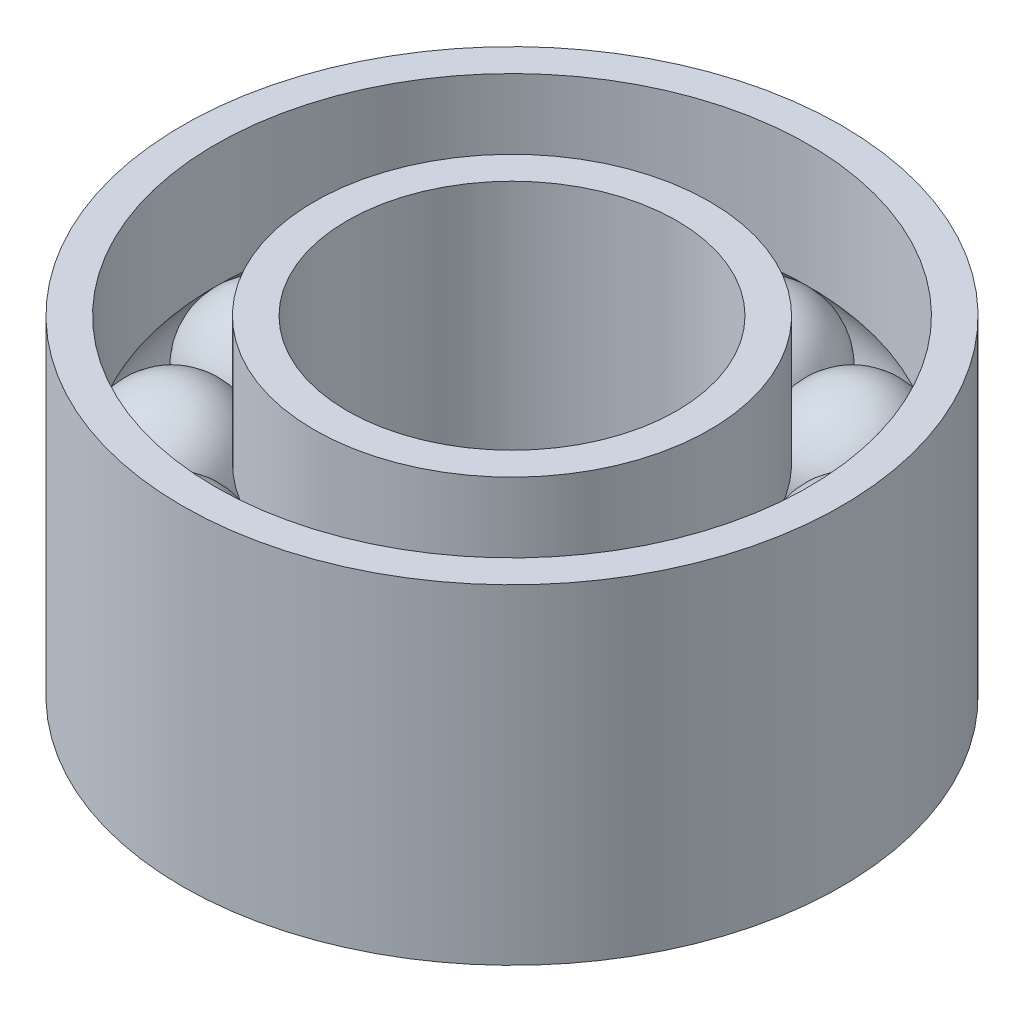
SolidWorks part; units mm, degrees
ref_plane "Front Plane" through (0, 0, 0) normal (0, 0, 1) x (1, 0, 0)
ref_plane "Top Plane" through (0, 0, 0) normal (0, 1, 0) x (1, 0, 0)
ref_plane "Right Plane" through (0, 0, 0) normal (1, 0, 0) x (0, 0, -1)
sketch "Sketch1" plane through (0, 0, 0) normal (0, 0, 1) x (1, 0, 0)
  line L0 (-6.35, 6.35) -> (-12.7, -6.35) construction
  line L1 (-7.62, 6.35) -> (-6.35, 6.35)
  line L2 (-7.62, 6.35) -> (-7.62, 1.4377)
  line L3 (-7.62, -6.35) -> (-6.35, -6.35)
  line L4 (-6.35, 6.35) -> (-6.35, -6.35)
  line L5 (-7.62, 6.35) -> (-6.35, -6.35) construction
  line L6 (-7.62, -6.35) -> (-6.35, 6.35) construction
  line L7 (-12.7, 6.35) -> (-11.43, 6.35)
  line L8 (-12.7, 6.35) -> (-12.7, -6.35)
  line L9 (-12.7, -6.35) -> (-11.43, -6.35)
  line L10 (-11.43, 6.35) -> (-11.43, 1.6105)
  line L11 (-12.7, 6.35) -> (-11.43, -6.35) construction
  line L12 (-12.7, -6.35) -> (-11.43, 6.35) construction
  line L13 (-11.43, -1.9145) -> (-11.43, -6.35)
  line L14 (-7.62, -1.7417) -> (-7.62, -6.35)
  arc A0 (-11.43, 1.6105) -> (-11.43, -1.9145) centre (-9.601, -0.152) ccw
  arc A1 (-7.62, -1.7417) -> (-7.62, 1.4377) centre (-9.601, -0.152) ccw
  point P0 (-6.985, 0)
  point P5 (-12.065, 0)
  dimension "D5" = 5.08
  dimension "D1" = 12.7
  dimension "D2" = 1.27
  dimension "D3" = 12.7
  dimension "D4" = 6.35
  dimension "D6" = 9.601
sketch "Sketch2" plane through (0, 0, 0) normal (0, 0, 1) x (1, 0, 0)
  line L0 (-9.601, 2.388) -> (-9.601, -2.692)
  arc A0 (-9.601, 2.388) -> (-9.601, -2.692) centre (-9.601, -0.152) cw
  dimension "D1" = 2.54
revolve "Revolve1" add sketch "Sketch2" angle 360 about L0
ref_axis "Axis1" through (0, 6.985, 0) along (0, -1, 0)
revolve "Revolve2" add sketch "Sketch1" angle 360 about axis through (0, 6.985, 0) along (0, -1, 0)
pattern_circular "CirPattern1" count 8 over 360 about axis through (0, 6.985, 0) along (0, -1, 0) of "Revolve1"
pattern_circular "CirPattern3" count 12 every 30 about axis through (0, 0, 0) along (0, 1, 0) of "Revolve1"
